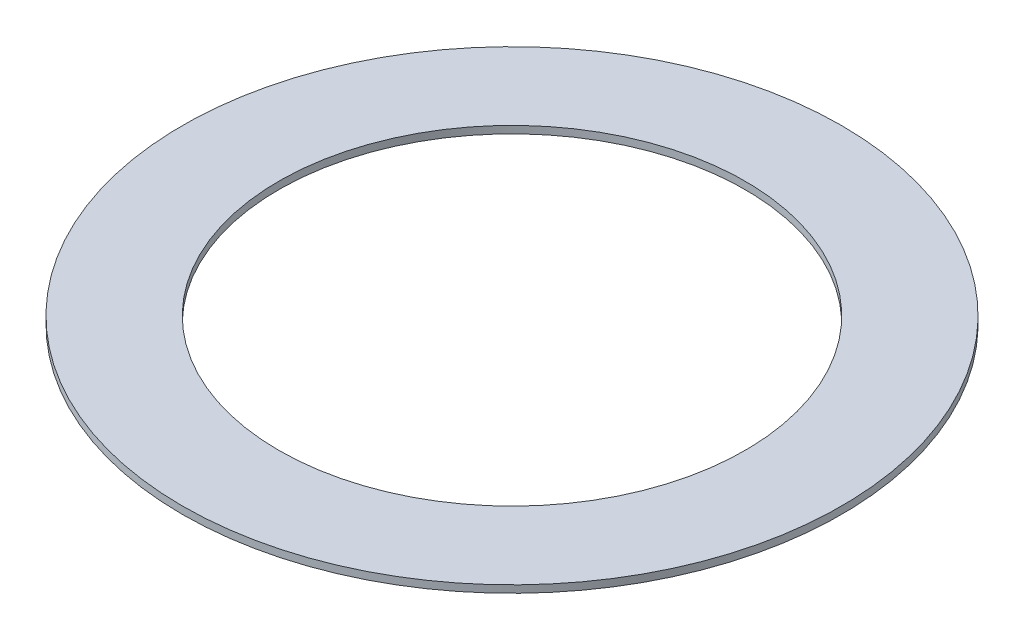
SolidWorks part; units mm, degrees
material "Oak"
ref_plane "Front Plane" through (0, 0, 0) normal (0, 0, 1) x (1, 0, 0)
ref_plane "Top Plane" through (0, 0, 0) normal (0, 1, 0) x (1, 0, 0)
ref_plane "Right Plane" through (0, 0, 0) normal (1, 0, 0) x (0, 0, -1)
sketch "Sketch1" plane through (0, 0, 0) normal (0, 1, 0) x (1, 0, 0)
  circle A0 centre (0, 0) radius 76.2
  circle A1 centre (0, 0) radius 107.696
  dimension "D1" = 152.4
  dimension "D2" = 215.392
extrude "Boss-Extrude1" add sketch "Sketch1" along normal blind 2.4
